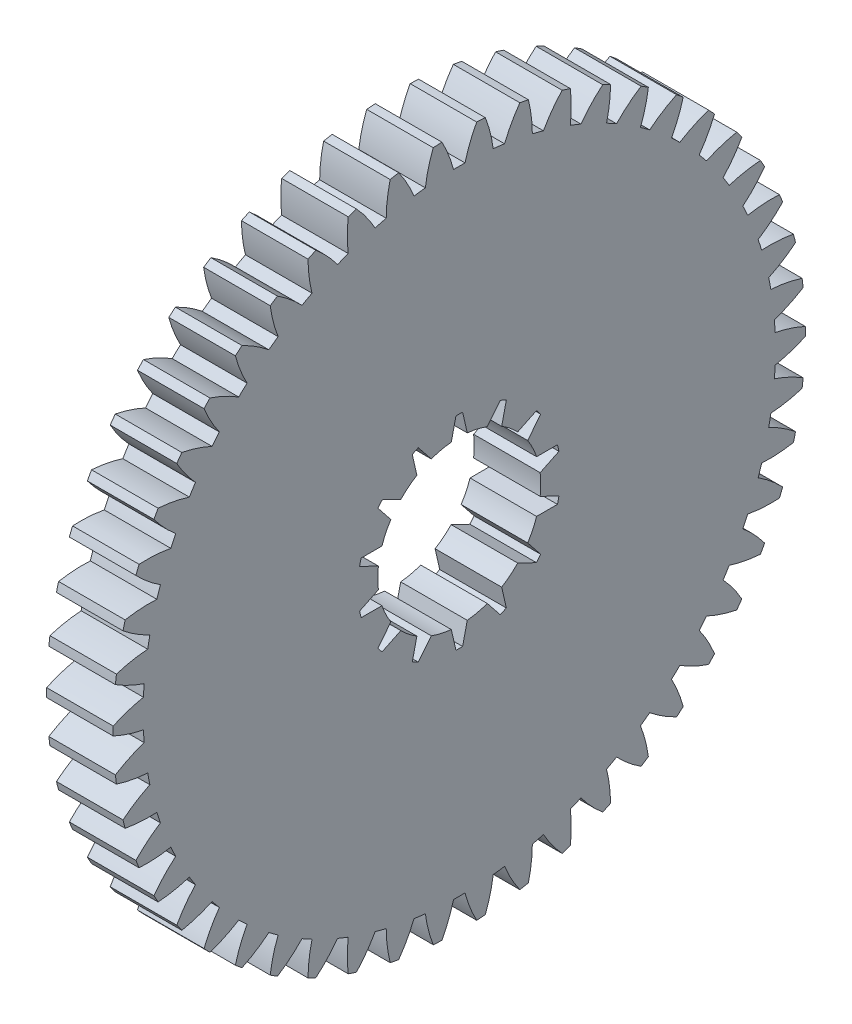
SolidWorks part; units mm, degrees
ref_plane "Plane1" through (0, 0, 0) normal (0, 0, 1) x (1, 0, 0)
ref_plane "Plane2" through (0, 0, 0) normal (0, 1, 0) x (1, 0, 0)
ref_plane "Plane3" through (0, 0, 0) normal (1, 0, 0) x (0, 0, -1)
other "Configuration Table"
sketch "HoldingSke" plane through (0, 0, 0) normal (0, 1, 0) x (1, 0, 0)
  line L0 (0, 0) -> (0.3214, -0.383)
  line L1 (-15, 0) -> (100, 0) construction
  line L2 (0, 0) -> (-2.1039, 2.3779)
  line L3 (0, 0) -> (-11.863, 4.5341)
  line L4 (0, 0) -> (5.5511, 6.6156)
  line L5 (0, 0) -> (-46.8476, -17.4728)
  line L6 (0, 0) -> (-8.2896, -5.593)
  line L7 (-2.1039, 2.3779) -> (8.6586, 51.2059)
  line L8 (-76.2, 54.61) -> (-73.4, 54.61)
  line L9 (-71.009, 38.7566) -> (-53.1078, 45.2721)
  line L10 (-76.2, 71.12) -> (104.1128, 71.12)
  line L11 (0, 0) -> (-10, 0)
  line L12 (-76.2, 101.6) -> (-76.133, 101.6)
  line L13 (24.9733, 27.94) -> (52.9518, 28.4284)
  line L14 (24.9733, 27.94) -> (24.9743, 27.94)
  line L15 (24.9733, 27.94) -> (100.4006, 29.5858)
  line L16 (-63.627, -2) -> (-12.827, -2)
  circle A0 centre (0, 0) radius 10
  circle A1 centre (0, 0) radius 37.5
  circle A2 centre (0, 0) radius 37.5
  circle A3 centre (0, 0) radius 10
  dimension "MHD" = 75
  dimension "Hub_dia" = 75
  dimension "Bore" = 20
  dimension "MBD" = 20
  dimension "Num_teeth" = 50
  dimension "Pitch" = 0.5
  dimension "Overall_len" = 50
  dimension "Show_teeth" = 50
  dimension "Thickness" = 10
  dimension "OAL" = 50.0001
  dimension "T_dim" = 2.8
  dimension "Ap" = 20
  dimension "H" = 19.05
  dimension "Pitch_radius" = 180.3128
  dimension "Width" = 10
  dimension "Backlash" = 0.067
  dimension "Addendum_fac" = 1
  dimension "Dedendum_fac" = 1.25
  dimension "Clearance_fac" = 0.25
  dimension "Dedendum_add" = 0.001
  dimension "Module" = 2
sketch "BasProSke" plane through (0, 0, 0) normal (0, 1, 0) x (1, 0, 0)
  line L0 (-10, 0) -> (60, 0) construction
  line L1 (0, 0) -> (0, 52)
  line L2 (0, 0) -> (10, 0)
  line L3 (10, 0) -> (10, 52)
  line L4 (10, 52) -> (0, 52)
  dimension "Thickness" = 10
  dimension "Diameter" = 104
revolve "Base-Revolve" add sketch "BasProSke" angle 360 about L0
sketch "TooCutSke" plane through (0, 0, 0) normal (1, 0, 0) x (0, 0, -1)
  line L1 (0, 0) -> (0, 107) construction
  line L2 (0, 0) -> (-1.6878, 49.9715) construction
  line L3 (0, 0) -> (-6.2764, 99.7605) construction
  line L4 (-1.6878, 49.9715) -> (-3.1382, 49.8803) construction
  arc A0 (0.8606, 47.4912) -> (-0.8606, 47.4912) centre (0, 0) ccw
  arc A1 (2.629, 51.9589) -> (-2.629, 51.9589) centre (0, 0) ccw
  circle A2 centre (0, 0) radius 50 construction
  circle A3 centre (0, 0) radius 46.9846 construction
  arc A4 (-0.8606, 47.4912) -> (-2.629, 51.9589) centre (-20.2064, 42.4176) ccw
  arc A5 (2.629, 51.9589) -> (0.8606, 47.4912) centre (20.2064, 42.4176) ccw
  dimension "Root_dia" = 94.998
  dimension "Overcut_dia" = 104.0508
  dimension "Pitch_dia" = 100
  dimension "Base_dia" = 93.9693
  dimension "Flank_rad" = 20
  dimension "Half_ang" = 3.6
  dimension "Half_CT" = 1.4533
extrude "ToothCut" cut sketch "TooCutSke" along normal through all
fillet "Breaks" [suppressed] radius 0.04
fillet "RootFillets" [suppressed] radius 0.501
pattern_circular "TeethCuts" count 50 every 7.2 about axis through (-10, 0, 0) along (1, 0, 0) of "ToothCut", "RootFillets", "Breaks"
sketch "HubNeaOneSke" plane through (0, 0, 0) normal (-1, 0, 0) x (0, 0, 1)
  circle A0 centre (0, 0) radius 37.5
  dimension "Diameter" = 75
extrude "HubNearOne" [suppressed] add sketch "HubNeaOneSke" along normal blind 40.0001
sketch "HubNeaBotSke" plane through (0, 0, 0) normal (-1, 0, 0) x (0, 0, 1)
  circle A0 centre (0, 0) radius 37.5
  dimension "Diameter" = 75
extrude "HubNearBoth" [suppressed] add sketch "HubNeaBotSke" along normal blind 20
ref_plane "FarPln" through (10, 0, 0) normal (1, 0, 0) x (0, 0, -1)
sketch "HubFarSke" plane through (10, 0, 0) normal (1, 0, 0) x (0, 0, -1)
  circle A0 centre (0, 0) radius 37.5
  dimension "Diameter" = 75
extrude "HubFar" [suppressed] add sketch "HubFarSke" along normal blind 20
sketch "BorSke" plane through (0, 0, 0) normal (1, 0, 0) x (0, 0, -1)
  circle A0 centre (0, 0) radius 10
  dimension "Diameter" = 20
extrude "Bore" cut sketch "BorSke" along normal mid plane 100.0001
sketch "KeySke" plane through (0, 0, 0) normal (1, 0, 0) x (0, 0, -1)
  line L0 (-3, 0) -> (-3, 12.8)
  line L1 (-3, 12.8) -> (3, 12.8)
  line L2 (3, 12.8) -> (3, 0)
  line L3 (0, 0) -> (0, 34) construction
  line L4 (-3, 0) -> (3, 0)
  dimension "Offset" = 12.8
  dimension "Width" = 6
extrude "Keyway" [suppressed] cut sketch "KeySke" along normal mid plane 100.0001
pattern_circular "Keyway2" [suppressed] count 2 every 90 about axis through (-10, 0, 0) along (1, 0, 0)
sketch "Esquisse1" plane through (10, 0, 0) normal (1, 0, 0) x (0, 0, -1)
  line L0 (0, 0) -> (0, 12.25) construction
  line L1 (-0.5, 15.2418) -> (-1.2, 12.1911)
  line L2 (0.5, 15.2418) -> (1.2, 12.1911)
  line L3 (6.1627, 13.9493) -> (4.2083, 11.5044)
  line L4 (7.0637, 13.5154) -> (6.3707, 10.4631)
  line L5 (11.6048, 9.894) -> (8.7832, 8.5392)
  line L6 (12.2283, 9.1122) -> (10.2796, 6.6628)
  line L7 (14.7484, 3.8791) -> (11.6184, 3.8827)
  line L8 (14.9709, 2.9042) -> (12.1525, 1.5429)
  line L9 (14.9709, -2.9042) -> (12.1525, -1.5429)
  line L10 (14.7484, -3.8791) -> (11.6184, -3.8827)
  line L11 (12.2283, -9.1122) -> (10.2796, -6.6628)
  line L12 (11.6048, -9.894) -> (8.7832, -8.5392)
  line L13 (7.0637, -13.5154) -> (6.3707, -10.4631)
  line L14 (6.1627, -13.9493) -> (4.2083, -11.5044)
  line L15 (0.5, -15.2418) -> (1.2, -12.1911)
  line L16 (-0.5, -15.2418) -> (-1.2, -12.1911)
  line L17 (-6.1627, -13.9493) -> (-4.2083, -11.5044)
  line L18 (-7.0637, -13.5154) -> (-6.3707, -10.4631)
  line L19 (-11.6048, -9.894) -> (-8.7832, -8.5392)
  line L20 (-12.2283, -9.1122) -> (-10.2796, -6.6628)
  line L21 (-14.7484, -3.8791) -> (-11.6184, -3.8827)
  line L22 (-14.9709, -2.9042) -> (-12.1525, -1.5429)
  line L23 (-14.9709, 2.9042) -> (-12.1525, 1.5429)
  line L24 (-14.7484, 3.8791) -> (-11.6184, 3.8827)
  line L25 (-12.2283, 9.1122) -> (-10.2796, 6.6628)
  line L26 (-11.6048, 9.894) -> (-8.7832, 8.5392)
  line L27 (-7.0637, 13.5154) -> (-6.3707, 10.4631)
  line L28 (-6.1627, 13.9493) -> (-4.2083, 11.5044)
  line L29 (0, 15.25) -> (0, 19.1139) construction
  arc A1 (0.5, 15.2418) -> (-0.5, 15.2418) centre (0, 0) ccw
  arc A3 (7.0637, 13.5154) -> (6.1627, 13.9493) centre (0, 0) ccw
  arc A5 (12.2283, 9.1122) -> (11.6048, 9.894) centre (0, 0) ccw
  arc A7 (14.9709, 2.9042) -> (14.7484, 3.8791) centre (0, 0) ccw
  arc A9 (14.7484, -3.8791) -> (14.9709, -2.9042) centre (0, 0) ccw
  arc A11 (11.6048, -9.894) -> (12.2283, -9.1122) centre (0, 0) ccw
  arc A13 (6.1627, -13.9493) -> (7.0637, -13.5154) centre (0, 0) ccw
  arc A15 (-0.5, -15.2418) -> (0.5, -15.2418) centre (0, 0) ccw
  arc A17 (-7.0637, -13.5154) -> (-6.1627, -13.9493) centre (0, 0) ccw
  arc A19 (-12.2283, -9.1122) -> (-11.6048, -9.894) centre (0, 0) ccw
  arc A21 (-14.9709, -2.9042) -> (-14.7484, -3.8791) centre (0, 0) ccw
  arc A23 (-14.7484, 3.8791) -> (-14.9709, 2.9042) centre (0, 0) ccw
  arc A25 (-11.6048, 9.894) -> (-12.2283, 9.1122) centre (0, 0) ccw
  arc A27 (-6.1627, 13.9493) -> (-7.0637, 13.5154) centre (0, 0) ccw
  arc A28 (-6.3707, 10.4631) -> (-8.7832, 8.5392) centre (0, 0) ccw
  arc A30 (-1.2, 12.1911) -> (-4.2083, 11.5044) centre (0, 0) ccw
  arc A31 (4.2083, 11.5044) -> (1.2, 12.1911) centre (0, 0) ccw
  arc A32 (8.7832, 8.5392) -> (6.3707, 10.4631) centre (0, 0) ccw
  arc A33 (11.6184, 3.8827) -> (10.2796, 6.6628) centre (0, 0) ccw
  arc A34 (12.1525, -1.5429) -> (12.1525, 1.5429) centre (0, 0) ccw
  arc A35 (10.2796, -6.6628) -> (11.6184, -3.8827) centre (0, 0) ccw
  arc A36 (6.3707, -10.4631) -> (8.7832, -8.5392) centre (0, 0) ccw
  arc A37 (1.2, -12.1911) -> (4.2083, -11.5044) centre (0, 0) ccw
  arc A38 (-4.2083, -11.5044) -> (-1.2, -12.1911) centre (0, 0) ccw
  arc A39 (-8.7832, -8.5392) -> (-6.3707, -10.4631) centre (0, 0) ccw
  arc A40 (-11.6184, -3.8827) -> (-10.2796, -6.6628) centre (0, 0) ccw
  arc A41 (-12.1525, 1.5429) -> (-12.1525, -1.5429) centre (0, 0) ccw
  arc A42 (-10.2796, 6.6628) -> (-11.6184, 3.8827) centre (0, 0) ccw
  point P7 (0, 15.25)
  point P8 (0, 12.25)
  point P64 (0, 0)
  dimension "D2" = 30.5
  dimension "D3" = 0.5
  dimension "D4" = 1.2
  dimension "D5" = 14
extrude "Enlèv. mat.-Extru.1" cut sketch "Esquisse1" against normal blind 10
equation "' \"Module@HoldingSke\" = 6.35"
equation "' \"Num_teeth@HoldingSke\" = 12"
equation "' \"Ap@HoldingSke\" =  20"
equation "' \"Ap@HoldingSke\" = 20"
equation "' \"Width@HoldingSke\" = 0.5 * 25.4"
equation "' \"Hub_dia@HoldingSke\"= 1 * 25.4"
equation "' \"Hub_dia@HoldingSke\" = 1 * 25.4"
equation "' \"Overall_len@HoldingSke\" = 1.0 * 25.4"
equation "' \"Bore@HoldingSke\" = 0.75 * 25.4"
equation "' \"T_dim@HoldingSke\" = 0.1 * 25.4"
equation "' \"Width@KeySke\" = 0.25 * 25.4"
equation "' \"Show_teeth@HoldingSke\" = 13"
equation "' \"Backlash@HoldingSke\" = 0.009 * 25.4"
equation "' \"Addendum_fac@HoldingSke\" = 1.0"
equation "' \"Dedendum_fac@HoldingSke\" = 1.25"
equation "' \"Dedendum_add@HoldingSke\" = 0.00005 * 25.4"
equation "' \"Clearance_fac@HoldingSke\" = 0.25"
equation "\"Pitch@HoldingSke\" = 1 / \"Module@HoldingSke\""
equation "\"Overcut_dia@TooCutSke\" = (\"Num_teeth@HoldingSke\" + 2 * \"Addendum_fac@HoldingSke\") / \"Pitch@HoldingSke\" + 0.002 * 25.4"
equation "\"Pitch_dia@TooCutSke\" = \"Num_teeth@HoldingSke\" / \"Pitch@HoldingSke\""
equation "\"Base_dia@TooCutSke\" = \"Num_teeth@HoldingSke\" / \"Pitch@HoldingSke\" * cos((\"Ap@HoldingSke\"  * 3.14159265 / 180))"
equation "\"Root_dia@TooCutSke\" = (\"Num_teeth@HoldingSke\" + 2) / \"Pitch@HoldingSke\" - 2 * (\"Addendum_fac@HoldingSke\" + \"Dedendum_fac@HoldingSke\") / \"Pitch@HoldingSke\" - \"Dedendum_add@HoldingSke\" * 2"
equation "\"Half_ang@TooCutSke\" = 180 / \"Num_teeth@HoldingSke\""
equation "\"Half_CT@TooCutSke\" = \"Num_teeth@HoldingSke\" / \"Pitch@HoldingSke\" * sin((3.14159265 / 2 / \"Num_teeth@HoldingSke\")) / 2 - 7 * \"Backlash@HoldingSke\" / 4"
equation "\"Flank_rad@TooCutSke\" = \"Num_teeth@HoldingSke\" / \"Pitch@HoldingSke\" / 5"
equation "\"Radius@RootFillets\" = \"Clearance_fac@HoldingSke\" / \"Pitch@HoldingSke\" + \"Dedendum_add@HoldingSke\""
equation "\"Break_rad@Breaks\" = 0.02 / \"Pitch@HoldingSke\""
equation "\"Thickness@HoldingSke\" = \"Width@HoldingSke\""
equation "\"OAL@HoldingSke\" = \"Thickness@HoldingSke\""
equation "\"MHD@HoldingSke\" = (\"Num_teeth@HoldingSke\" + 2) / \"Pitch@HoldingSke\" - 2 * (\"Addendum_fac@HoldingSke\" + \"Dedendum_fac@HoldingSke\")  / \"Pitch@HoldingSke\" - \"Dedendum_add@HoldingSke\" * 2"
equation "\"MBD@HoldingSke\" = (\"Num_teeth@HoldingSke\" + 2) / \"Pitch@HoldingSke\" - 2 * (\"Addendum_fac@HoldingSke\" + \"Dedendum_fac@HoldingSke\")  / \"Pitch@HoldingSke\" - \"Dedendum_add@HoldingSke\" * 2 - 0.002 * 25.4"
equation "\"MHD@HoldingSke\" = ((sgn( \"MHD@HoldingSke\" - \"Hub_dia@HoldingSke\" )-1)*( \"MHD@HoldingSke\" - \"Hub_dia@HoldingSke\" ))/-2+ \"Hub_dia@HoldingSke\""
equation "\"MBD@HoldingSke\" = ((sgn( \"MBD@HoldingSke\" - \"Bore@HoldingSke\" )-1)*( \"MBD@HoldingSke\" - \"Bore@HoldingSke\" ))/-2+ \"Bore@HoldingSke\""
equation "\"OAL@HoldingSke\" = ((sgn( \"OAL@HoldingSke\" - \"Overall_len@HoldingSke\" )+1)*( \"OAL@HoldingSke\" - \"Overall_len@HoldingSke\" ))/2 + \"Overall_len@HoldingSke\" + 0.000002 * 25.4"
equation "\"Num_teeth@TeethCuts\" = int( \"Show_teeth@HoldingSke\" ) + 1"
equation "\"Num_teeth@TeethCuts\" = ((sgn( \"Num_teeth@TeethCuts\" - \"Num_teeth@HoldingSke\" )-1)*( \"Num_teeth@TeethCuts\" - \"Num_teeth@HoldingSke\" ))/-2+ \"Num_teeth@HoldingSke\""
equation "\"Num_teeth@TeethCuts\" = ((sgn( \"Num_teeth@TeethCuts\" - 2.0)+1)*( \"Num_teeth@TeethCuts\" - 2.0))/2 +2.0"
equation "\"Angle@TeethCuts\" = 360.0 / \"Num_teeth@HoldingSke\""
equation "\"Diameter@BasProSke\" = (\"Num_teeth@HoldingSke\" + 2 * \"Addendum_fac@HoldingSke\") / \"Pitch@HoldingSke\""
equation "\"Thickness@BasProSke\"  = \"Thickness@HoldingSke\""
equation "' \"Fillet_rad@BasProSke\" =  \"Thickness@HoldingSke\" * 0.05"
equation "' \"Fillet_rad@BasProSke\" = \"Thickness@HoldingSke\" * 0.05"
equation "\"MHD@HoldingSke\" = ((sgn( \"MHD@HoldingSke\" - \"Root_dia@TooCutSke\" )-1)*( \"MHD@HoldingSke\" - \"Root_dia@TooCutSke\" ))/-2+ \"Root_dia@TooCutSke\""
equation "\"Diameter@HubNeaOneSke\" = \"MHD@HoldingSke\""
equation "\"Length@HubNearOne\" = \"OAL@HoldingSke\" - \"Thickness@BasProSke\""
equation "\"Diameter@HubNeaBotSke\" = \"MHD@HoldingSke\""
equation "\"Length@HubNearBoth\" = ( \"OAL@HoldingSke\" - \"Thickness@BasProSke\" ) / 2.0"
equation "\"Thickness@FarPln\" = \"Thickness@BasProSke\""
equation "\"Diameter@HubFarSke\" = \"MHD@HoldingSke\""
equation "\"Length@HubFar\" = ( \"OAL@HoldingSke\" - \"Thickness@BasProSke\" ) / 2.0"
equation "\"Diameter@BorSke\" = \"MBD@HoldingSke\""
equation "\"D1@Bore\" = \"OAL@HoldingSke\" * 2.0"
equation "\"D1@Keyway\" = \"OAL@HoldingSke\" * 2.0"
equation "\"Offset@KeySke\" = \"T_dim@HoldingSke\" + \"MBD@HoldingSke\" / 2.0"
